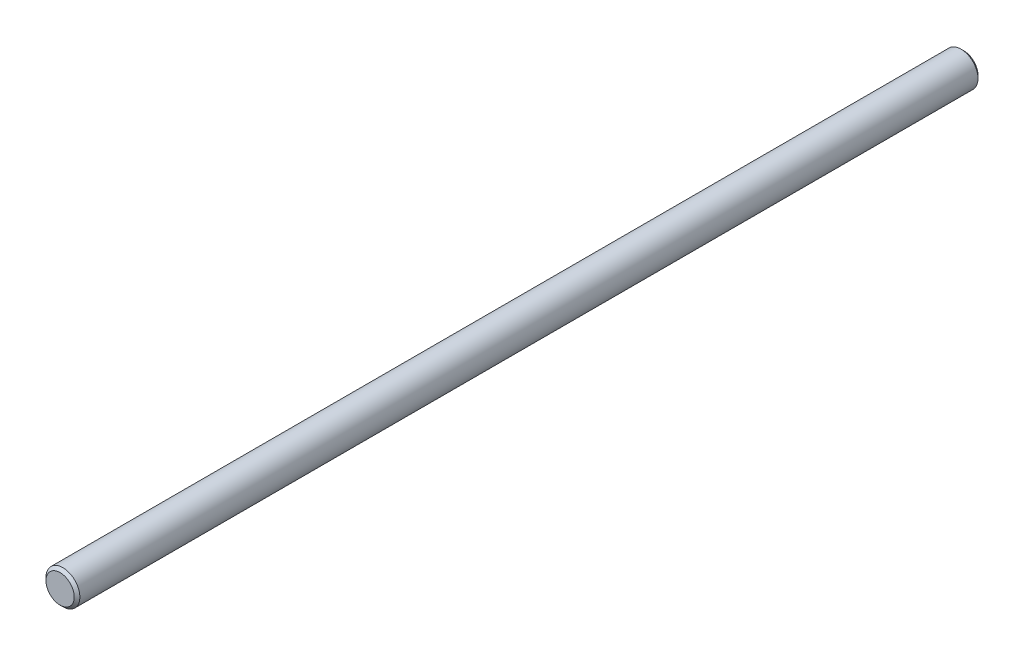
SolidWorks part; units mm, degrees
ref_plane "Front Plane" through (0, 0, 0) normal (0, 0, 1) x (1, 0, 0)
ref_plane "Top Plane" through (0, 0, 0) normal (0, 1, 0) x (1, 0, 0)
ref_plane "Right Plane" through (0, 0, 0) normal (1, 0, 0) x (0, 0, -1)
sketch "Sketch1" plane through (0, 0, 0) normal (0, 0, 1) x (1, 0, 0)
  line L0 (0, -55) -> (0, 55) construction
  circle A0 centre (0, 3.6208) radius 3
  dimension "D1" = 6
extrude "Boss-Extrude1" add sketch "Sketch1" along normal blind 160
chamfer "Chamfer1" distance 0.5 angle 45 1 edges at (3, 3.6208, 160)
chamfer "Chamfer2" distance 0.5 angle 45 1 edges at (3, 3.6208, 0)
